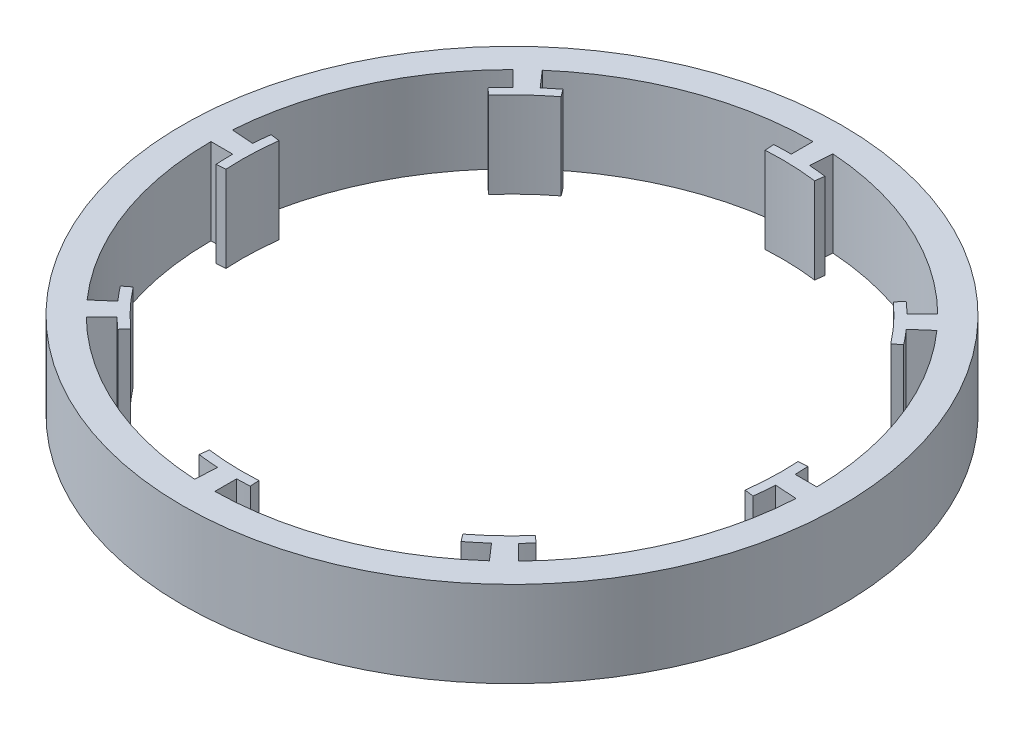
SolidWorks part; units mm, degrees
ref_plane "Front Plane" through (0, 0, 0) normal (0, 0, 1) x (1, 0, 0)
ref_plane "Top Plane" through (0, 0, 0) normal (0, 1, 0) x (1, 0, 0)
ref_plane "Right Plane" through (0, 0, 0) normal (1, 0, 0) x (0, 0, -1)
sketch "Sketch1" plane through (0, 0, 0) normal (0, 1, 0) x (1, 0, 0)
  line L0 (0, 97.45) -> (0, 105.05)
  line L1 (6.6281, 97.2243) -> (7.145, 104.8067)
  line L2 (68.4294, 69.3824) -> (73.8035, 74.7566)
  line L3 (72.9784, 64.5806) -> (78.7056, 69.5767)
  line L4 (97.4407, 1.3478) -> (105.0414, 1.3478)
  line L5 (97.3065, -5.2859) -> (104.8896, -5.8028)
  line L6 (70.0484, -67.7475) -> (75.4231, -73.1222)
  line L7 (65.2415, -72.3882) -> (70.2381, -78.116)
  line L8 (1.3478, -97.4407) -> (1.3478, -105.0414)
  line L9 (-5.3774, -97.3015) -> (-5.8944, -104.8845)
  line L10 (-68.4294, -69.3824) -> (-73.8035, -74.7566)
  line L11 (-73.0643, -64.4834) -> (-78.7915, -69.4796)
  line L12 (-97.45, 0) -> (-105.05, 0)
  line L13 (-97.2181, 6.7195) -> (-104.8005, 7.2365)
  line L14 (-68.7099, 69.1047) -> (-74.0839, 74.4787)
  line L15 (-63.8165, 73.6476) -> (-68.8125, 79.3747)
  line L16 (0, 0) -> (12.5511, 96.6384)
  line L17 (0, 0) -> (-5.9492, 97.2682)
  line L18 (0, 0) -> (77.2086, 59.4586)
  line L19 (0, 0) -> (64.5723, 72.9857)
  line L20 (0, 0) -> (96.6384, -12.5511)
  line L21 (0, 0) -> (97.2682, 5.9492)
  line L22 (0, 0) -> (59.4586, -77.2086)
  line L23 (0, 0) -> (72.9857, -64.5723)
  line L24 (0, 0) -> (-12.5511, -96.6384)
  line L25 (0, 0) -> (5.9492, -97.2682)
  line L26 (0, 0) -> (-77.2086, -59.4586)
  line L27 (0, 0) -> (-64.5723, -72.9857)
  line L28 (0, 0) -> (-96.6384, 12.5511)
  line L29 (0, 0) -> (-97.2682, -5.9492)
  line L30 (0, 0) -> (-59.4586, 77.2086)
  line L31 (0, 0) -> (-72.9857, 64.5723)
  circle A0 centre (0, 0) radius 115
  arc A1 (-74.0839, 74.4787) -> (-104.8005, 7.2365) centre (0, 0) ccw
  arc A3 (-68.7099, 69.1047) -> (-97.2181, 6.7195) centre (0, 0) ccw
  arc A4 (-97.45, 0) -> (-73.0643, -64.4834) centre (0, 0) ccw
  arc A5 (-68.4294, -69.3824) -> (-5.3774, -97.3015) centre (0, 0) ccw
  arc A8 (0, 105.05) -> (-68.8125, 79.3747) centre (0, 0) ccw
  arc A9 (73.8035, 74.7566) -> (7.145, 104.8067) centre (0, 0) ccw
  arc A10 (105.0414, 1.3478) -> (78.7056, 69.5767) centre (0, 0) ccw
  arc A11 (75.4231, -73.1222) -> (104.8896, -5.8028) centre (0, 0) ccw
  arc A12 (1.3478, -105.0414) -> (70.2381, -78.116) centre (0, 0) ccw
  arc A13 (-73.8035, -74.7566) -> (-5.8944, -104.8845) centre (0, 0) ccw
  arc A14 (-105.05, 0) -> (-78.7915, -69.4796) centre (0, 0) ccw
  arc A15 (0, 97.45) -> (-63.8165, 73.6476) centre (0, 0) ccw
  circle A16 centre (0, 0) radius 94.25
  arc A17 (1.3478, -97.4407) -> (65.2415, -72.3882) centre (0, 0) ccw
  arc A18 (70.0484, -67.7475) -> (97.3065, -5.2859) centre (0, 0) ccw
  arc A19 (97.4407, 1.3478) -> (72.9784, 64.5806) centre (0, 0) ccw
  arc A20 (68.4294, 69.3824) -> (6.6281, 97.2243) centre (0, 0) ccw
  point P54 (0, 0)
  point P56 (0, 0)
  dimension "D1" = 230
  dimension "D2" = 105.05
  dimension "D3" = 188.5
  dimension "D6" = 194.9
  dimension "D4" = 3.9
  dimension "D7" = 3.5
  dimension "D8" = 3.5
  dimension "D5" = 8
  dimension "D9" = 8
extrude "Boss-Extrude1" add sketch "Sketch1" along normal blind 30
